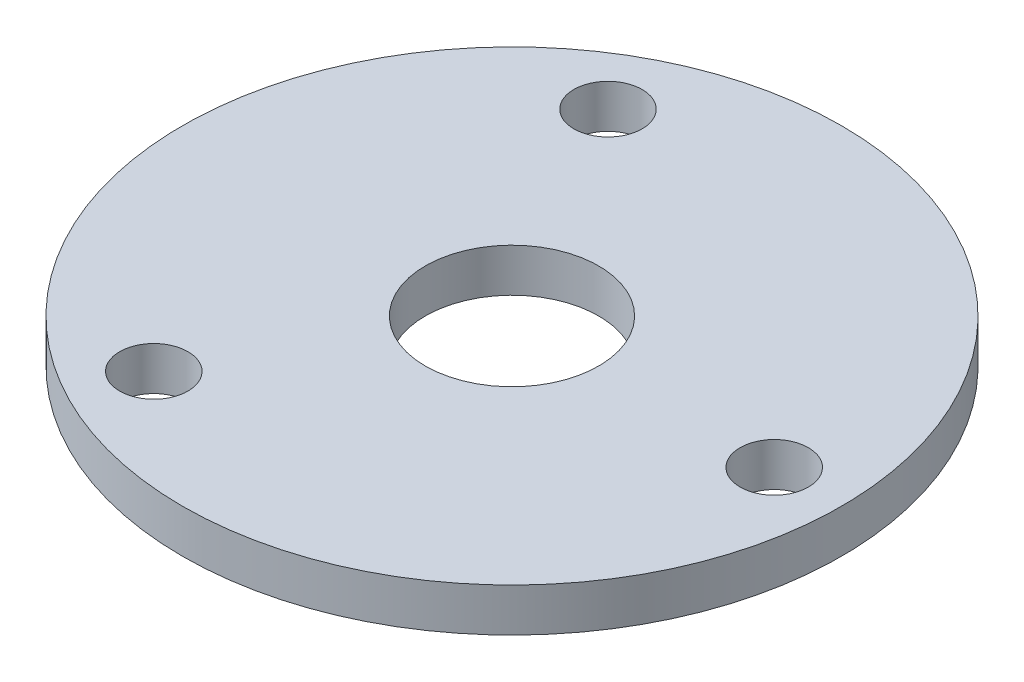
SolidWorks part; units mm, degrees
material "Acrylic (Medium-high impact)"
ref_plane "Front Plane" through (0, 0, 0) normal (0, 0, 1) x (1, 0, 0)
ref_plane "Top Plane" through (0, 0, 0) normal (0, 1, 0) x (1, 0, 0)
ref_plane "Right Plane" through (0, 0, 0) normal (1, 0, 0) x (0, 0, -1)
sketch "Sketch1" plane through (0, 0, 0) normal (0, 1, 0) x (1, 0, 0)
  line L0 (13, 0) -> (25.4, 0) construction
  line L2 (19.2, 0) -> (9.6, 16.6277) construction
  line L3 (9.6, 16.6277) -> (-9.6, 16.6277) construction
  line L4 (-9.6, 16.6277) -> (-19.2, 0) construction
  line L5 (-19.2, 0) -> (-9.6, -16.6277) construction
  line L6 (-9.6, -16.6277) -> (9.6, -16.6277) construction
  line L7 (9.6, -16.6277) -> (19.2, 0) construction
  circle A0 centre (0, 0) radius 24.13
  circle A1 centre (0, 0) radius 25.4 construction
  circle A2 centre (0, 0) radius 13 construction
  circle A3 centre (19.2, 0) radius 2.5
  circle A4 centre (0, 0) radius 16.6277 construction
  circle A5 centre (-9.6, 16.6277) radius 2.5
  circle A6 centre (-9.6, -16.6277) radius 2.5
  circle A7 centre (0, 0) radius 6.35
  dimension "D1" = 48.26
  dimension "D2" = 50.8
  dimension "D3" = 26
  dimension "D4" = 5
  dimension "D5" = 5
  dimension "D6" = 5
  dimension "D7" = 12.7
extrude "Boss-Extrude1" add sketch "Sketch1" along normal blind 3.175
